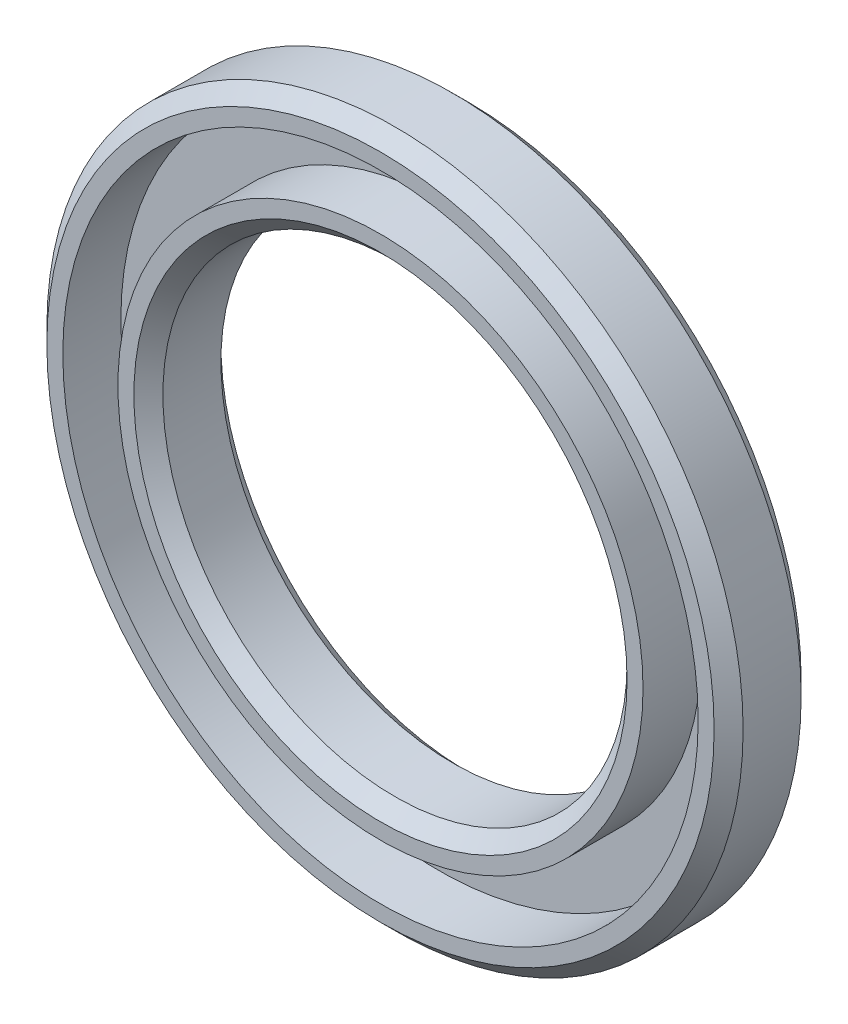
SolidWorks part; units mm, degrees
material "1060 Alloy"
ref_plane "Front Plane" through (0, 0, 0) normal (0, 0, 1) x (1, 0, 0)
ref_plane "Top Plane" through (0, 0, 0) normal (0, 1, 0) x (1, 0, 0)
ref_plane "Right Plane" through (0, 0, 0) normal (1, 0, 0) x (0, 0, -1)
sketch "Sketch1" plane through (0, 0, 0) normal (0, 0, 1) x (1, 0, 0)
  circle A0 centre (0, 0) radius 12
  circle A1 centre (0, 0) radius 8
  dimension "D1" = 24
  dimension "D2" = 16
extrude "Boss-Extrude1" add sketch "Sketch1" along normal blind 3
chamfer "Chamfer1" distance 0.5 angle 45 4 edges at (12, 0, 0) (8, 0, 0) (8, 0, 3) (12, 0, 3)
sketch "Sketch2" plane through (0, 0, 3) normal (0, 0, 1) x (1, 0, 0)
  circle A0 centre (0, 0) radius 10.95
  circle A1 centre (0, 0) radius 9.05
  dimension "D1" = 18.1
  dimension "D2" = 21.9
extrude "Cut-Extrude1" cut sketch "Sketch2" against normal blind 2
